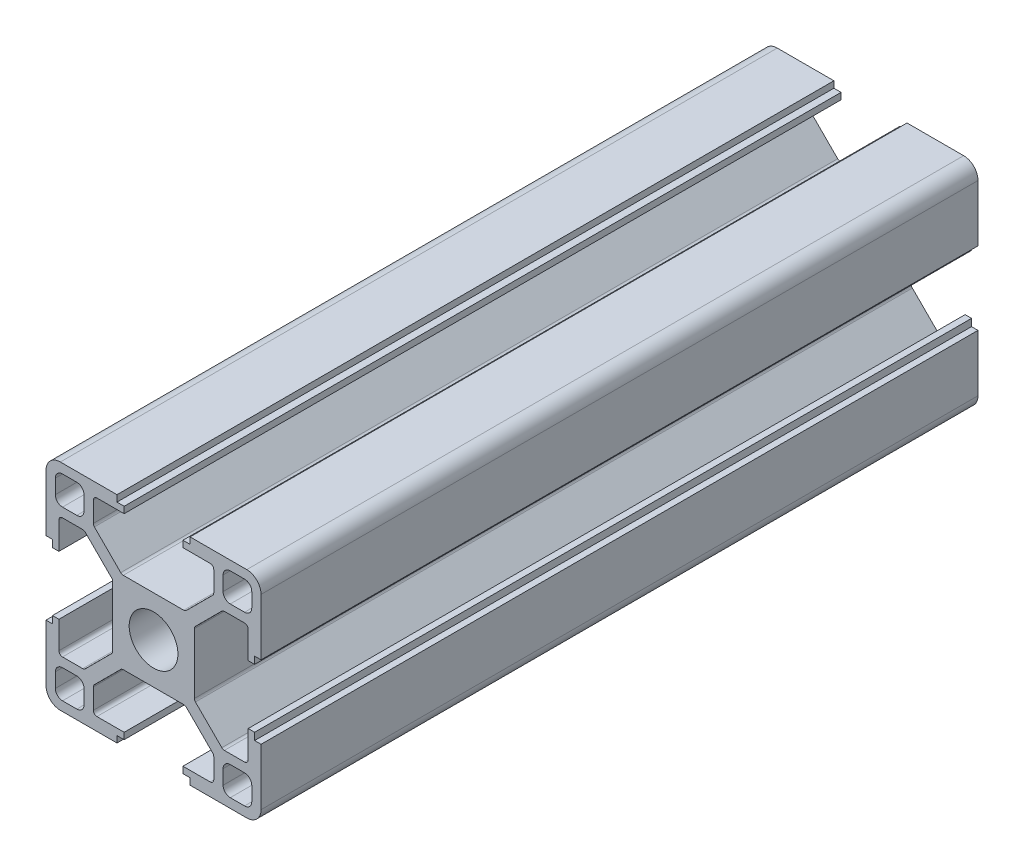
SolidWorks part; units mm, degrees
ref_plane "前视基准面" through (0, 0, 0) normal (0, 0, 1) x (1, 0, 0)
ref_plane "上视基准面" through (0, 0, 0) normal (0, 1, 0) x (1, 0, 0)
ref_plane "右视基准面" through (0, 0, 0) normal (1, 0, 0) x (0, 0, -1)
sketch "草图1" plane through (0, 0, 0) normal (0, 0, 1) x (1, 0, 0)
  line L0 (0, 0) -> (0, 65.3905) construction
  line L1 (0, 0) -> (64.2648, 0) construction
  line L2 (0, 0) -> (79.9729, 79.9729) construction
  line L3 (5.7, 0) -> (5.7, 4.4272)
  line L4 (5.7, 4.4272) -> (9.6728, 8.4)
  line L5 (9.6728, 8.4) -> (13.2, 8.4)
  line L6 (13.2, 8.4) -> (13.2, 4.1)
  line L7 (13.2, 4.1) -> (14.1, 4.1)
  line L8 (14.1, 4.1) -> (14.1, 5.1)
  line L9 (14.1, 5.1) -> (15, 5.1)
  line L10 (15, 5.1) -> (15, 15)
  line L11 (5.1, 15) -> (15, 15)
  line L12 (5.1, 14.1) -> (5.1, 15)
  line L13 (4.1, 14.1) -> (5.1, 14.1)
  line L14 (4.1, 13.2) -> (4.1, 14.1)
  line L15 (8.4, 13.2) -> (4.1, 13.2)
  line L16 (8.4, 9.6728) -> (8.4, 13.2)
  line L17 (4.4272, 5.7) -> (8.4, 9.6728)
  line L18 (0, 5.7) -> (4.4272, 5.7)
  line L20 (9.7, 9.7) -> (13.7, 9.7)
  line L21 (9.7, 9.7) -> (9.7, 13.7)
  line L22 (9.7, 13.7) -> (13.7, 13.7)
  line L23 (13.7, 9.7) -> (13.7, 13.7)
  line L24 (9.7, 9.7) -> (13.7, 13.7) construction
  line L25 (9.7, 13.7) -> (13.7, 9.7) construction
  line L26 (0, 5.7) -> (0, 0)
  line L27 (0, 0) -> (5.7, 0)
  point P9 (11.7, 11.7)
  dimension "D1" = 45
  dimension "D2" = 5.7
  dimension "D3" = 1.8
  dimension "D4" = 0.9
  dimension "D5" = 8.2
  dimension "D6" = 10.2
  dimension "D7" = 1.8
  dimension "D8" = 15
  dimension "D9" = 16.8
  dimension "D10" = 4
  dimension "D11" = 1.3
extrude "凸台-拉伸1" add sketch "草图1" along normal blind 100 contours L3 L4 L5 L6 L7 L8 L9 L10 L11 L12 L13 L14 L15 L16 L17 L18 L26 L27
fillet "圆角1" radius 1 4 edges at (9.7, 9.7, 50) (13.7, 9.7, 50) (9.7, 13.7, 50) (13.7, 13.7, 50)
fillet "圆角2" radius 2 1 edges at (15, 15, 50)
fillet "圆角3" radius 0.5 6 edges at (5.7, 4.4272, 50) (4.4272, 5.7, 50) (8.4, 13.2, 50) (8.4, 9.6728, 50) (9.6728, 8.4, 50) (13.2, 8.4, 50)
pattern_circular "阵列(圆周)1" count 4 over 360 about axis through (0, 0, 0) along (0, 0, 1) of "圆角2", "圆角3", "凸台-拉伸1", "圆角1"
sketch "草图2" plane through (0, 0, 100) normal (0, 0, 1) x (1, 0, 0)
  circle A0 centre (0, 0) radius 3.4
  dimension "D1" = 6.8
extrude "切除-拉伸1" cut sketch "草图2" against normal through all
cosmetic thread "装饰螺纹线1" parameters "D1"=20, "D2"=8
sketch "草图3" plane through (0, 0, 0) normal (1, 0, 0) x (0, 0, -1)
  line L0 (-123.9675, 0) -> (18.956, 0) construction
  line L1 (-100, 15) -> (0, 15) construction
  line L2 (0, -15) -> (-100, -15) construction
  line L3 (-100, -4.2201) -> (-100, 4.2201) construction
  circle A0 centre (-80.8, 0) radius 4
  dimension "D1" = 8
  dimension "D2" = 19.2
extrude "切除-拉伸2" cut sketch "草图3" against normal mid plane 30
sketch "草图9" plane through (0, 0, 0) normal (0, 0, -1) x (-1, 0, 0)
  circle A0 centre (0, 0) radius 4
  dimension "D1" = 8
extrude "切除-拉伸3" [suppressed] cut sketch "草图9" against normal blind 20
